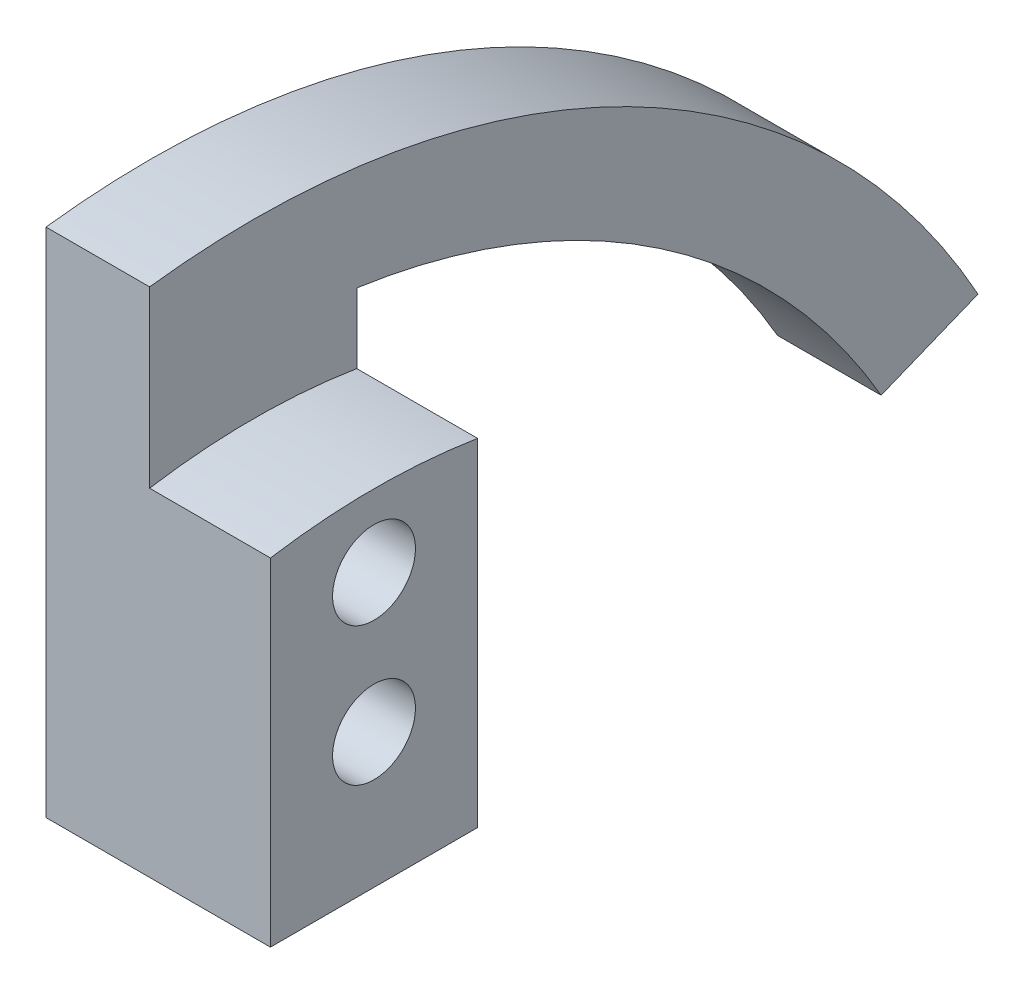
SolidWorks part; units mm, degrees
ref_plane "Alzado" through (0, 0, 0) normal (0, 0, 1) x (1, 0, 0)
ref_plane "Planta" through (0, 0, 0) normal (0, 1, 0) x (1, 0, 0)
ref_plane "Vista lateral" through (0, 0, 0) normal (1, 0, 0) x (0, 0, -1)
sketch "Croquis1" plane through (0, 0, 0) normal (1, 0, 0) x (0, 0, -1)
  line L0 (0, 0) -> (0, 8.45) construction
  line L1 (-1.5, 4.5) -> (1.5, 4.5)
  line L2 (1.5, 4.5) -> (1.5, 10.3923)
  line L3 (0, 0) -> (4.6646, 0) construction
  line L4 (-1.5, 4.5) -> (-1.5, 11.9059)
  line L5 (0, 0) -> (12.6167, 7.2843) construction
  line L7 (9.0933, 5.25) -> (10.496, 5.8167)
  circle A0 centre (0, 8.45) radius 0.6
  circle A1 centre (0, 6.45) radius 0.6
  arc A2 (9.0933, 5.25) -> (1.5, 10.3923) centre (0, 0) ccw
  arc A3 (10.496, 5.8167) -> (-1.5, 11.9059) centre (0, 0) ccw
  point P7 (10.8253, 6.25)
  point P15 (10.9304, 6.0643)
  point P16 (0, 0)
  point P17 (10.9432, 6.0413)
  point P18 (10.9412, 6.0449)
  dimension "D2" = 2
  dimension "D6" = 6.45
  dimension "D7" = 24
  dimension "D1" = 1.2
  dimension "D8" = 21
  dimension "D3" = 3
  dimension "D4" = 1.5
  dimension "D5" = 4.5
  dimension "D9" = 30
  dimension "D10" = 8
extrude "Saliente-Extruir1" add sketch "Croquis1" along normal blind 1.5
sketch "Croquis2" plane through (1.5, 0, 0) normal (1, 0, 0) x (0, 0, -1)
  line L0 (-1.5, 4.5) -> (1.5, 4.5)
  line L1 (1.5, 4.5) -> (1.5, 9.3808)
  line L4 (-1.5, 9.3808) -> (-1.5, 4.5)
  circle A0 centre (0, 6.45) radius 0.6 construction
  circle A1 centre (0, 8.45) radius 0.6 construction
  circle A2 centre (0, 6.45) radius 0.6
  circle A3 centre (0, 8.45) radius 0.6
  arc A4 (1.5, 9.3808) -> (-1.5, 9.3808) centre (0, 0) ccw
  dimension "D1" = 9.5
extrude "Saliente-Extruir2" add sketch "Croquis2" along normal blind 1.75
